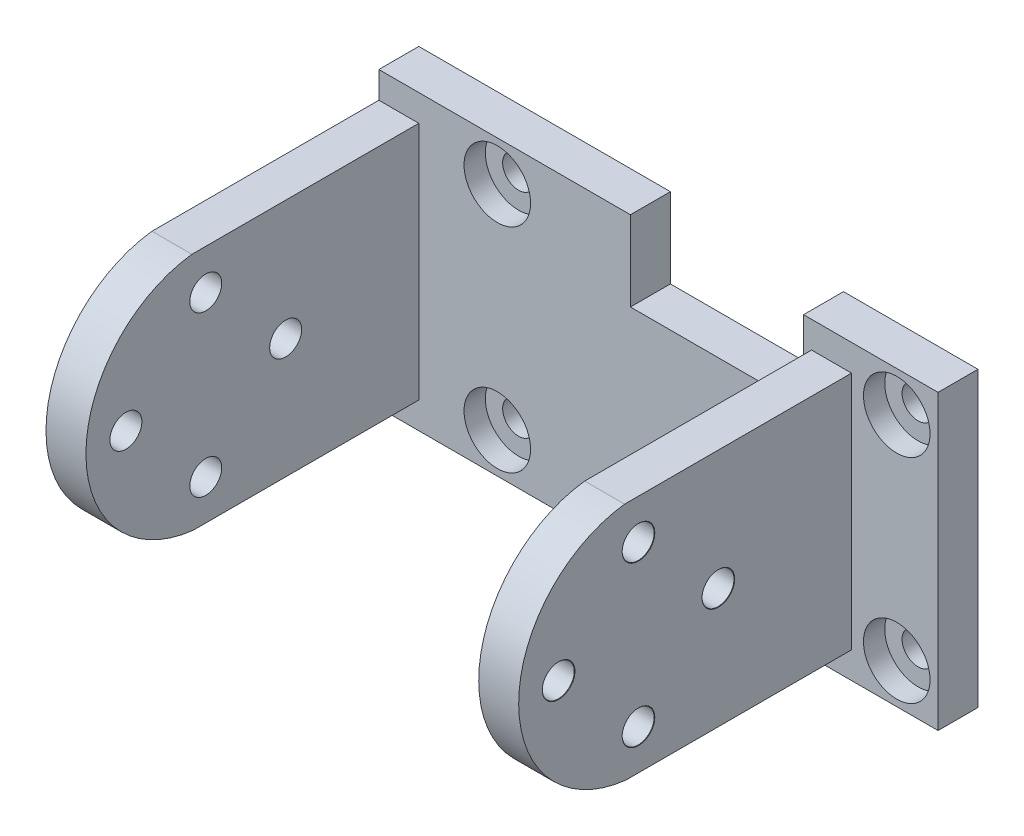
SolidWorks part; units mm, degrees
ref_plane "Front Plane" through (0, 0, 0) normal (0, 0, 1) x (1, 0, 0)
ref_plane "Top Plane" through (0, 0, 0) normal (0, 1, 0) x (1, 0, 0)
ref_plane "Right Plane" through (0, 0, 0) normal (1, 0, 0) x (0, 0, -1)
ref_plane "Plane1" through (0, 0, 47.8926) normal (0, 0, 1) x (1, 0, 0)
sketch "Sketch1" plane through (0, 0, 47.8926) normal (0, 0, 1) x (1, 0, 0)
  line L0 (29.75, 233.2226) -> (-12.25, 233.2226)
  line L1 (-12.25, 233.2226) -> (-12.25, 211.2226)
  line L2 (-12.25, 211.2226) -> (29.75, 211.2226)
  line L3 (29.75, 211.2226) -> (29.75, 233.2226)
extrude "Boss-Extrude1" add sketch "Sketch1" against normal blind 3
sketch "Sketch2" plane through (0, 0, 44.8926) normal (0, 0, -1) x (-1, 0, 0)
  line L0 (-6.6467, 233.2226) -> (-19.6467, 233.2226)
  line L1 (-19.6467, 233.2226) -> (-19.6467, 227.2226)
  line L2 (-19.6467, 227.2226) -> (-6.6467, 227.2226)
  line L3 (-6.6467, 227.2226) -> (-6.6467, 233.2226)
extrude "Cut-Extrude1" cut sketch "Sketch2" against normal through all
sketch "Sketch3" plane through (0, 0, 44.8926) normal (0, 0, -1) x (-1, 0, 0)
  line L0 (-19.6467, 211.2226) -> (-6.6467, 211.2226)
  line L1 (-6.6467, 211.2226) -> (-6.6467, 217.2226)
  line L2 (-6.6467, 217.2226) -> (-19.6467, 217.2226)
  line L3 (-19.6467, 217.2226) -> (-19.6467, 211.2226)
extrude "Cut-Extrude2" cut sketch "Sketch3" against normal through all
ref_plane "Plane2" through (-12.25, 0, 0) normal (-1, 0, 0) x (0, -1, 0)
sketch "Sketch4" plane through (-12.25, 0, 0) normal (-1, 0, 0) x (0, -1, 0)
  line L0 (-231.2226, 64.9357) -> (-231.2226, 47.8926)
  line L1 (-231.2226, 47.8926) -> (-213.2226, 47.8926)
  line L2 (-213.2226, 47.8926) -> (-213.2226, 64.8395)
  arc A0 (-213.2226, 64.8395) -> (-231.2226, 64.9357) centre (-222.2283, 63.8306) ccw
extrude "Boss-Extrude2" add sketch "Sketch4" against normal blind 3
ref_plane "Plane3" through (23.25, 0, 0) normal (1, 0, 0) x (0, 0, -1)
sketch "Sketch5" plane through (23.25, 0, 0) normal (1, 0, 0) x (0, 0, -1)
  line L0 (-64.8395, 213.2226) -> (-47.8926, 213.2226)
  line L1 (-47.8926, 213.2226) -> (-47.8926, 231.2226)
  line L2 (-47.8926, 231.2226) -> (-64.9357, 231.2226)
  arc A0 (-64.9357, 231.2226) -> (-64.8395, 213.2226) centre (-63.8306, 222.2283) ccw
extrude "Boss-Extrude3" add sketch "Sketch5" against normal blind 3
hole_wizard "M2 Clearance Hole1" positions "Sketch7" profile "Sketch6" hole size "M2" standard "ANSI Metric" end condition through all
sketch "Sketch7" plane through (23.25, 0, 0) normal (1, 0, 0) x (0, 0, -1)
  point P0 (-63.8928, 228.2222)
  point P1 (-69.8926, 222.2224)
  point P2 (-63.8928, 216.2226)
  point P3 (-57.893, 222.2224)
sketch "Sketch6" plane through (23.25, 228.2222, 63.8928) normal (0, 1, 0) x (0, 0, -1)
  line L0 (0, 0) -> (0, 35.5)
  line L1 (0, 35.5) -> (1.2, 35.5)
  line L2 (1.2, 35.5) -> (1.2, 0.025)
  line L3 (1.2, 0.025) -> (1.225, 0)
  line L5 (1.225, 0) -> (0, 0)
  line L6 (-1.2, 0.025) -> (-1.225, 0) construction
  line L11 (0, -6.35) -> (0, 107.95) construction
  dimension "Thru Hole Dia." = 2.4
  dimension "Thru Hole Depth" = 35.5
  dimension "Near C'Sink Dia." = 2.45
  dimension "Near C'Sink Angle" = 90
hole_wizard "CBORE for M2 Pan Head Machine Screw1" positions "Sketch9" profile "Sketch8" counterbore size "M2" standard "ANSI Metric" end condition through all
sketch "Sketch9" plane through (0, 0, 47.8926) normal (0, 0, 1) x (1, 0, 0)
  point P0 (-3.3533, 230.215)
  point P1 (-3.3533, 214.215)
  point P2 (26.6467, 214.215)
  point P3 (26.6467, 230.215)
sketch "Sketch8" plane through (-3.3533, 230.215, 47.8926) normal (1, 0, 0) x (0, -1, 0)
  line L0 (0, 0) -> (0, 3)
  line L1 (0, 3) -> (1.2, 3)
  line L3 (1.2, 3) -> (1.2, 1.6)
  line L4 (1.2, 1.6) -> (2.5, 1.6)
  line L5 (2.5, 1.6) -> (2.5, 0)
  line L7 (2.5, 0) -> (0, 0)
  line L11 (0, -6.35) -> (0, 107.95) construction
  dimension "Thru Hole Dia." = 2.4
  dimension "Thru Hole Depth" = 3
  dimension "C'Bore Dia." = 5
  dimension "C'Bore Depth" = 1.6
ref_plane "Plane4" through (5.5, 0, 0) normal (1, 0, 0) x (0, 0, -1)
